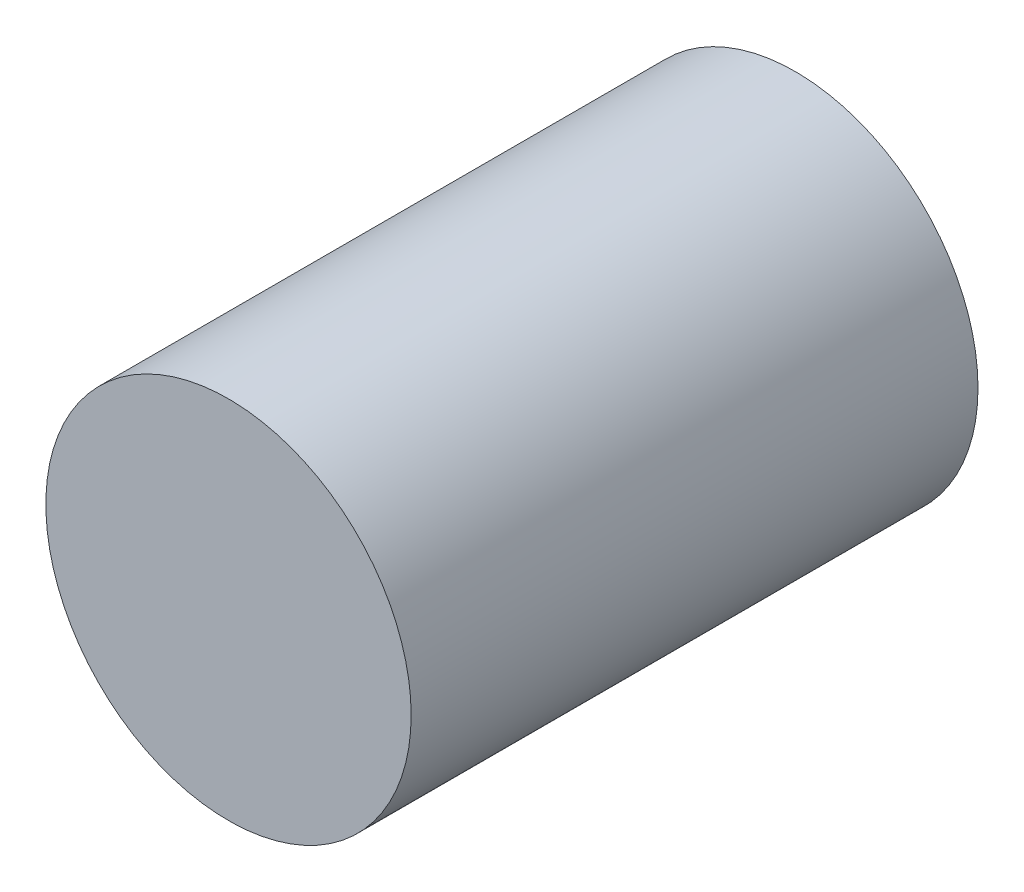
SolidWorks part; units mm, degrees
ref_plane "Front Plane" through (0, 0, 0) normal (0, 0, 1) x (1, 0, 0)
ref_plane "Top Plane" through (0, 0, 0) normal (0, 1, 0) x (1, 0, 0)
ref_plane "Right Plane" through (0, 0, 0) normal (1, 0, 0) x (0, 0, -1)
sketch "Sketch1" plane through (0, 0, 0) normal (0, 0, 1) x (1, 0, 0)
  circle A0 centre (0, 0) radius 5.8
  dimension "D2" = 11.6
extrude "Boss-Extrude1" add sketch "Sketch1" against normal blind 18
sketch "Sketch2" plane through (0, 0, -18) normal (0, 0, -1) x (-1, 0, 0)
  circle A0 centre (0, 0) radius 4
  dimension "D1" = 8
extrude "Cut-Extrude1" cut sketch "Sketch2" against normal blind 12
